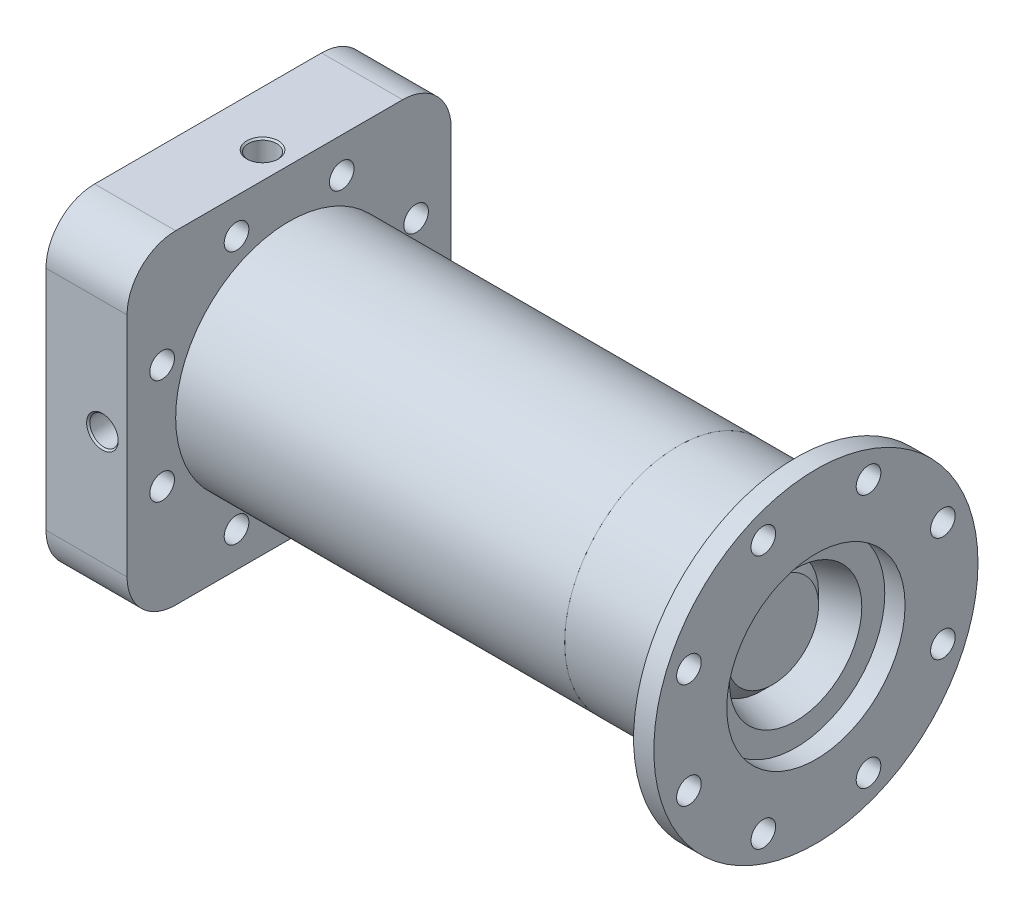
SolidWorks part; units mm, degrees
other "TC"
other "Injector "
other "Volume "
other "Aft O Ring"
other "Forward O ring" parameters "D11"=9.6936, "D1"=8.9273, "D2"=33.6348, "D3"=26.5468, "D4"=23.315, "D5"=33.6348, "D6"=5.8865, "D7"=63.1196, "D8"=7.0953, "D9"=1.4619, "D10"=3.7307, "D12"=6.1926, "D13"=4.361, "D14"=3.81, "D15"=11.3511, "D16"=3.7343, "D17"=3.7343, "D18"=7.0449
ref_plane "Front Plane" through (0, 0, 0) normal (0, 0, 1) x (1, 0, 0)
ref_plane "Top Plane" through (0, 0, 0) normal (0, 1, 0) x (1, 0, 0)
ref_plane "Right Plane" through (0, 0, 0) normal (1, 0, 0) x (0, 0, -1)
sketch "Chamber Revolve" plane through (0, 0, 0) normal (0, 0, 1) x (1, 0, 0)
  line L1 (223.9623, 63.5) -> (223.9623, 25.908)
  line L4 (189.463, 17.9788) -> (173.5582, 33.8836)
  line L5 (173.5582, 33.8836) -> (0, 33.8836)
  line L10 (0, 33.8836) -> (0, 42.5196)
  line L11 (0, 63.5) -> (10.16, 63.5)
  line L12 (10.16, 63.5) -> (10.16, 47.5996)
  line L13 (0, 0) -> (66.3921, 0) construction
  line L15 (191.9165, 17.3214) -> (223.9623, 25.908)
  line L16 (10.16, 47.5996) -> (24.13, 47.5996)
  line L17 (24.13, 47.5996) -> (24.13, 63.5)
  line L18 (24.13, 63.5) -> (223.9623, 63.5)
  line L19 (190.5, 16.9418) -> (191.9165, 17.3214) construction
  line L20 (190.5, 16.9418) -> (189.463, 17.9788) construction
  line L21 (0, 48.5902) -> (3.8608, 48.5902)
  line L22 (3.8608, 48.5902) -> (3.8608, 42.5196)
  line L23 (3.8608, 42.5196) -> (0, 42.5196)
  line L24 (0, 48.5902) -> (0, 63.5)
  arc A0 (189.463, 17.9788) -> (191.9165, 17.3214) centre (191.2591, 19.7748) ccw
  dimension "D11" = 2.54
  dimension "D2" = 67.7672
  dimension "D3" = 51.816
  dimension "D6" = 45
  dimension "D13" = 10.16
  dimension "D8" = 33.8836
  dimension "D9" = 33.4623
  dimension "D7" = 13.716
  dimension "D15" = 13.97
  dimension "D5" = 190.5
  dimension "D4" = 15
  dimension "D18" = 6.0706
  dimension "D12" = 127
revolve "Revolve1" add sketch "Chamber Revolve" angle 360 about L13
fillet "Fillet1" radius 1.27 2 edges at (24.13, 0, 47.5996) (10.16, 0, 47.5996)
sketch "Sketch2" plane through (0, 0, 0) normal (-1, 0, 0) x (0, 0, 1)
  line L0 (0, 0) -> (-24.3004, 58.6664) construction
  line L1 (0, 0) -> (0, 56.6825) construction
  circle A0 centre (-21.7732, 52.565) radius 3.81
  circle A1 centre (0, 0) radius 63.5 construction
  dimension "D2" = 7.62
  dimension "D1" = 6.604
  dimension "D3" = 22.5
extrude "Cut-Extrude1" cut sketch "Sketch2" against normal up to next
pattern_circular "CirPattern1" count 8 over 360 about axis through (0, 0, 0) along (1, 0, 0) of "Cut-Extrude1"
sketch "Sketch4" plane through (0, 0, 0) normal (-1, 0, 0) x (0, 0, 1)
  circle A0 centre (0, 0) radius 63.5
  circle A1 centre (0, 0) radius 63.5 construction
extrude "Boss-Extrude1" add sketch "Sketch4" along normal blind 31.75 separate body
sketch "Sketch5" plane through (0, 0, 0) normal (1, 0, 0) x (0, 0, -1)
  circle A0 centre (21.7732, 52.565) radius 3.81 construction
  circle A1 centre (21.7732, 52.565) radius 3.81
sketch "Sketch11" plane through (-31.75, 0, 0) normal (-1, 0, 0) x (0, 0, 1)
  line L1 (-63.5, -63.5) -> (63.5, -63.5)
  line L2 (-63.5, -63.5) -> (-63.5, 63.5)
  line L3 (-63.5, 63.5) -> (63.5, 63.5)
  line L4 (63.5, -63.5) -> (63.5, 63.5)
  circle A0 centre (0, 0) radius 63.5 construction
  circle A1 centre (0, 0) radius 63.5
  point P6 (0, 63.5)
  point P9 (-63.5, 0)
  circle M18 centre (0, 0) radius 63.5
  dimension "D1" = 127
extrude "Boss-Extrude2" add sketch "Sketch11" against normal up to surface (31.75 mm away) contours L3 L2 L1 M18 | L1 L4 L3 M18 | L4 L3 M18 | L2 L1 M18 up to face at (0, 0, 63.5)
sketch "Sketch12" plane through (0, 0, 0) normal (1, 0, 0) x (0, 0, -1)
  circle A0 centre (0, 0) radius 24.13
  dimension "D1" = 48.26
extrude "Cut-Extrude4" cut sketch "Sketch12" against normal blind 16.51
sketch "Sketch13" plane through (0, 0, 63.5) normal (0, 0, 1) x (1, 0, 0)
  line L1 (0, 63.5) -> (0, -63.5) construction
  line L2 (73.3425, 0) -> (-73.3425, 0) construction
  circle A0 centre (-9.652, 0) radius 1.9685
  dimension "D1" = 3.937
  dimension "D2" = 9.652
extrude "Cut-Extrude5" cut sketch "Sketch13" against normal up to next and the other way through all
sketch "Sketch14" plane through (0, 0, 0) normal (1, 0, 0) x (0, 0, -1)
  line L0 (-63.5, 63.5) -> (63.5, 63.5) construction
  line L1 (-63.5, -63.5) -> (63.5, -63.5) construction
  line L2 (-12.7, 63.5) -> (-63.5, 63.5)
  line L3 (-63.5, 63.5) -> (-63.5, -63.5)
  line L4 (-63.5, -63.5) -> (-12.7, -63.5)
  arc A0 (-12.7, 63.5) -> (-12.7, -63.5) centre (0, 0) ccw
  circle A1 centre (0, 0) radius 63.5 construction
  dimension "D1" = 12.7
chamfer "Chamfer1" distance 4.572 angle 45 1 edges at (0, 0, -24.13)
sketch "Sketch18" plane through (0, 0, 63.5) normal (0, 0, 1) x (1, 0, 0)
  point P0 (-9.652, 0)
hole_wizard "7/16 (0.4375) Diameter Hole1" positions "Sketch18" profile "Sketch20" hole size "7/16" standard "ANSI Inch"
sketch "Sketch20" plane through (-9.652, 0, 63.5) normal (1, 0, 0) x (0, -1, 0)
  line L0 (0, 0) -> (0, 22.3885)
  line L1 (0, 22.3885) -> (5.5562, 19.05)
  line L2 (5.5562, 19.05) -> (5.5562, 0.635)
  line L3 (5.5562, 0.635) -> (6.1912, 0)
  line L5 (6.1912, 0) -> (0, 0)
  line L6 (-5.5562, 0.635) -> (-6.1912, 0) construction
  line L10 (0, 22.3885) -> (-5.5563, 19.05) construction
  line L11 (0, -6.35) -> (0, 107.95) construction
  dimension "Hole Dia." = 11.1125
  dimension "Hole Depth" = 19.05
  dimension "Near C'Sink Dia." = 12.3825
  dimension "Near C'Sink Angle" = 90
  dimension "Drill Angle" = 118
mirror "Mirror1" about plane through (0, 0, 0) normal (0, 0, 1) of "7/16 (0.4375) Diameter Hole1", "Cut-Extrude5"
sketch "Sketch21" plane through (0, 0, 0) normal (0, 1, 0) x (1, 0, 0)
  line L0 (0, 33.8836) -> (173.5582, 33.8836)
  line L1 (0, 42.5196) -> (0, -42.5196) construction
  line L2 (0, 33.8836) -> (0, -33.8836) construction
  line L3 (173.5582, -33.8836) -> (173.5582, 33.8836) construction
  line L4 (173.5582, 33.8836) -> (189.463, 17.9788)
  line L5 (189.463, -17.9788) -> (189.463, 17.9788) construction
  line L6 (189.463, 17.9788) -> (189.463, 0)
  line L10 (0, 0) -> (0, 33.8836)
  line L11 (0, 0) -> (189.463, 0)
  line L12 (189.463, 0) -> (214.4295, 0) construction
revolve "Revolve2" add sketch "Sketch21" angle 360 about L12
fillet "Fillet2" radius 0.889 2 edges at (3.8608, 0, 42.5196) (3.8608, 0, 48.5902)
sketch "Sketch22" plane through (-31.75, 0, 0) normal (-1, 0, 0) x (0, 0, 1)
  point P0 (0, -33.02)
  dimension "D1" = 33.02
hole_wizard "Ø6.7 (6.7) Diameter Hole1" positions "Sketch22" profile "Sketch23" hole size "Ø6.7" standard "ANSI Metric"
sketch "Sketch23" plane through (-31.75, -33.02, 0) normal (0, 1, 0) x (0, 0, 1)
  line L0 (0, 0) -> (0, 15.2209)
  line L1 (0, 15.2209) -> (3.35, 13.208)
  line L2 (3.35, 13.208) -> (3.35, 0.4)
  line L3 (3.35, 0.4) -> (3.75, 0)
  line L5 (3.75, 0) -> (0, 0)
  line L6 (-3.35, 0.4) -> (-3.75, 0) construction
  line L10 (0, 15.2209) -> (-3.35, 13.208) construction
  line L11 (0, -6.35) -> (0, 107.95) construction
  dimension "Hole Dia." = 6.7
  dimension "Hole Depth" = 13.208
  dimension "Near C'Sink Dia." = 7.5
  dimension "Near C'Sink Angle" = 90
  dimension "Drill Angle" = 118
mirror "Mirror2" about plane through (0, 0, 0) normal (0, 1, 0) of "Ø6.7 (6.7) Diameter Hole1"
sketch "Sketch24" plane through (0, 0, 0) normal (0, 1, 0) x (1, 0, 0)
  line L0 (-31.75, 63.5) -> (-31.75, -63.5) construction
  line L1 (-31.75, 7.1374) -> (-30.9581, 5.7658)
  line L2 (-30.9581, 5.7658) -> (-29.845, 5.7658)
  line L3 (-29.4858, 5.617) -> (-28.7329, 4.8641)
  line L4 (-28.7329, 4.8641) -> (-16.51, 4.8641)
  line L5 (-16.51, -24.13) -> (-16.51, 24.13) construction
  line L6 (-16.51, 4.8641) -> (-16.51, 0)
  line L7 (-16.51, 0) -> (-31.75, 0)
  line L8 (-31.75, 0) -> (-31.75, 7.1374)
  line L9 (-29.845, 5.7658) -> (-29.6346, 5.7658) construction
  line L10 (-29.6346, 5.7658) -> (-29.4858, 5.617) construction
  line L11 (-31.75, 0) -> (-56.3457, 0) construction
  arc A0 (-29.845, 5.7658) -> (-29.4858, 5.617) centre (-29.845, 5.2578) cw
  dimension "D2" = 0.508
  dimension "D1" = 60
  dimension "D3" = 4.8641
  dimension "D4" = 7.1374
  dimension "D5" = 5.7658
  dimension "D6" = 1.905
  dimension "D7" = 45
  dimension "D8" = 15.24
ref_axis "Axis1" through (223.9623, 0, 0) along (-1, 0, 0)
revolve "Cut-Revolve1" cut sketch "Sketch24" angle 360 about axis through (223.9623, 0, 0) along (-1, 0, 0)
fillet "Fillet3" radius 0.508 1 edges at (-30.9581, 0, -5.7658)
sketch "Sketch25" plane through (0, 0, 0) normal (0, 0, 1) x (1, 0, 0)
  line L0 (0, -63.5) -> (-31.75, -63.5) construction
  line L1 (0, -63.5) -> (-31.75, -63.5) construction
  line L2 (-4.318, -63.5) -> (-5.4699, -62.8349)
  line L3 (-5.588, -62.6304) -> (-5.588, -61.468)
  line L4 (-11.43, -26.67) -> (-9.398, -26.67)
  line L5 (-5.7368, -61.1088) -> (-6.604, -60.2416)
  line L6 (-6.604, -60.2416) -> (-6.604, -46.8376)
  line L7 (-11.43, -63.5) -> (-11.43, -26.67)
  line L8 (-16.51, -24.13) -> (-16.51, 24.13) construction
  line L9 (-6.604, -46.8376) -> (-9.398, -45.1588)
  line L10 (-9.398, -45.1588) -> (-9.398, -26.67)
  line L11 (-16.51, -24.13) -> (-16.51, 24.13) construction
  line L12 (-11.43, -63.5) -> (-4.318, -63.5)
  line L13 (-11.43, -63.5) -> (-11.43, -73.7659) construction
  arc A1 (-5.588, -61.468) -> (-5.7368, -61.1088) centre (-6.096, -61.468) ccw
  arc A2 (-5.4699, -62.8349) -> (-5.588, -62.6304) centre (-5.3518, -62.6304) cw
  dimension "D4" = 0.2362
  dimension "D6" = 0.508
  dimension "D1" = 7.112
  dimension "D2" = 5.08
  dimension "D3" = 60
  dimension "D5" = 5.842
  dimension "D7" = 45
  dimension "D8" = 2.032
  dimension "D9" = 4.826
  dimension "D10" = 16.6624
  dimension "D11" = 59
  dimension "D12" = 2.032
  dimension "D13" = 2.54
sketch "Sketch29" plane through (0, -63.5, 0) normal (0, -1, 0) x (-1, 0, 0)
  line L0 (0, -63.5) -> (0, 63.5) construction
  point P0 (10.414, 0)
  dimension "D1" = 10.414
hole_wizard "7/16 (0.4375) Diameter Hole2" positions "Sketch29" profile "Sketch30" hole size "7/16" standard "ANSI Inch"
sketch "Sketch30" plane through (-10.414, -63.5, 0) normal (1, 0, 0) x (0, 0, -1)
  line L0 (0, 0) -> (0, 22.3885)
  line L1 (0, 22.3885) -> (5.5562, 19.05)
  line L2 (5.5562, 19.05) -> (5.5562, 0.635)
  line L3 (5.5562, 0.635) -> (6.1913, 0)
  line L5 (6.1913, 0) -> (0, 0)
  line L6 (-5.5562, 0.635) -> (-6.1913, 0) construction
  line L10 (0, 22.3885) -> (-5.5563, 19.05) construction
  line L11 (0, -6.35) -> (0, 107.95) construction
  dimension "Hole Dia." = 11.1125
  dimension "Hole Depth" = 19.05
  dimension "Near C'Sink Dia." = 12.3825
  dimension "Near C'Sink Angle" = 90
  dimension "Drill Angle" = 118
sketch "Sketch31" plane through (0, -63.5, 0) normal (0, -1, 0) x (1, 0, 0)
  circle A0 centre (-10.414, 0) radius 1.5875
  dimension "D1" = 3.175
extrude "Cut-Extrude9" cut sketch "Sketch31" against normal up to surface (39.4223 mm away)
mirror "Mirror3" about plane through (0, 0, 0) normal (0, 1, 0) of "Cut-Extrude9", "7/16 (0.4375) Diameter Hole2"
delete or keep bodies "Body-Delete/Keep 1" type delete bodies bodies 103
sketch "Sketch37" plane through (0, 0, 0) normal (1, 0, 0) x (0, 0, -1)
  line L0 (-63.5, -63.5) -> (63.5, -63.5) construction
  line L1 (-63.5, 63.5) -> (63.5, 63.5) construction
  line L2 (63.5, 63.5) -> (63.5, -63.5) construction
  line L3 (-63.5, 63.5) -> (-63.5, -63.5) construction
  line L4 (-63.5, -63.5) -> (63.5, -63.5)
  line L5 (-63.5, 63.5) -> (63.5, 63.5)
  line L6 (63.5, 63.5) -> (63.5, -63.5)
  line L7 (-63.5, 63.5) -> (-63.5, -63.5)
  circle A0 centre (0, 0) radius 43.688
  dimension "D1" = 87.376
sketch "Sketch32" plane through (0, 0, 0) normal (1, 0, 0) x (0, 0, -1)
  circle A0 centre (0, 0) radius 44.45
  circle A1 centre (0, 0) radius 69.85
  dimension "D1" = 88.9
  dimension "D2" = 139.7
sketch "Sketch33" plane through (0, 0, 0) normal (1, 0, 0) x (0, 0, -1)
  circle A0 centre (0, 0) radius 34.925
  circle A1 centre (0, 0) radius 44.45
  dimension "D1" = 69.85
  dimension "D2" = 88.9
extrude "Boss-Extrude4" add sketch "Sketch33" along normal blind 152.4 separate body
sketch "Sketch34" plane through (0, 0, 0) normal (0, 0, 1) x (1, 0, 0)
  line L2 (152.4, 44.45) -> (152.4, 34.925)
  line L6 (152.4, 34.925) -> (164.992, 16.9418)
  line L7 (164.992, 16.9418) -> (198.4543, 25.908)
  line L8 (198.4543, 25.908) -> (198.4543, 44.45)
  line L9 (198.4543, 44.45) -> (152.4, 44.45)
  line L10 (154.0002, 0) -> (250.6574, 0) construction
  line L11 (152.4, -34.925) -> (152.4, 34.925) construction
  line L12 (152.4, -44.45) -> (152.4, 44.45) construction
  line L13 (152.4, -34.925) -> (152.4, 34.925) construction
  line L14 (152.4, -44.45) -> (152.4, 44.45) construction
  dimension "D1" = 33.8836
  dimension "D2" = 51.816
  dimension "D3" = 15
  dimension "D7" = 55
ref_axis "Axis2" through (152.4, 0, 0) along (-1, 0, 0)
revolve "Revolve3" add sketch "Sketch34" angle 360 about axis through (152.4, 0, 0) along (-1, 0, 0)
fillet "Fillet5" radius 1.27 1 edges at (164.992, 0, -16.9418)
sketch "Sketch35" plane through (0, 0, 0) normal (1, 0, 0) x (0, 0, -1)
  line L0 (0, 0) -> (0, 81.6848) construction
  line L1 (0, 0) -> (18.5655, 44.8211) construction
  line L2 (17.0103, 41.0664) -> (18.5655, 44.8211) construction
  circle A0 centre (18.5655, 44.8211) radius 4.064
  circle A1 centre (0, 0) radius 44.45 construction
  dimension "D1" = 8.128
  dimension "D2" = 22.5
  dimension "D3" = 4.064
fillet "Fillet6" radius 19.05 4 edges at (-15.875, -63.5, 63.5) (-15.875, -63.5, -63.5) (-15.875, 63.5, -63.5) (-15.875, 63.5, 63.5)
sketch "Sketch39" plane through (198.4543, 0, 0) normal (1, 0, 0) x (0, 0, -1)
  circle A0 centre (0, 0) radius 34.925
  circle A1 centre (0, 0) radius 63.5
  dimension "D1" = 69.85
  dimension "D2" = 127
extrude "Boss-Extrude6" add sketch "Sketch39" along normal blind 7.9375 separate body
sketch "Sketch40" plane through (198.4543, 0, 0) normal (-1, 0, 0) x (0, 0, 1)
  line L0 (0, 0) -> (0, 54.3419) construction
  line L1 (0, 0) -> (-20.6067, 49.7491) construction
  circle A0 centre (-20.6067, 49.7491) radius 4.826
  dimension "D2" = 9.652
  dimension "D1" = 22.5
  dimension "D3" = 53.848
extrude "Cut-Extrude13" cut sketch "Sketch40" along normal through all both and the other way through all
pattern_circular "CirPattern3" count 8 over 360 about axis through (0, 0, 0) along (1, 0, 0) of "Cut-Extrude13"
sketch "Sketch41" plane through (0, 0, 0) normal (0, 0, 1) x (1, 0, 0)
  line L0 (0, 37.338) -> (-2.1844, 37.338)
  line L1 (0, 44.45) -> (0, -44.45) construction
  line L2 (-2.6416, 37.7952) -> (-2.6416, 40.9702)
  line L3 (-2.1844, 41.4274) -> (0, 41.4274)
  line L4 (0, 0) -> (38.5106, 0) construction
  line L5 (-2.6416, 41.4274) -> (-2.1844, 41.4274) construction
  line L6 (-2.6416, 40.9702) -> (-2.6416, 41.4274) construction
  line L7 (-2.6416, 37.338) -> (-2.6416, 37.7952) construction
  line L8 (-2.1844, 37.338) -> (-2.6416, 37.338) construction
  line L9 (0, 37.338) -> (0, 41.4274)
  arc A0 (-2.1844, 41.4274) -> (-2.6416, 40.9702) centre (-2.1844, 40.9702) ccw
  arc A1 (-2.6416, 37.7952) -> (-2.1844, 37.338) centre (-2.1844, 37.7952) ccw
  point P15 (0, 41.4036)
  dimension "D4" = 0.4572
  dimension "D1" = 4.0894
  dimension "D2" = 2.6416
  dimension "D3" = 41.4274
revolve "Cut-Revolve2" cut sketch "Sketch41" angle 360 about L4
sketch "Sketch43" plane through (0, 0, 0) normal (0, 0, 1) x (1, 0, 0)
  circle A0 centre (-1.1621, 39.5944) radius 1.3347
sketch "Sketch44" plane through (0, 0, 0) normal (0, 0, 1) x (1, 0, 0)
  line L0 (-2.6416, -40.9702) -> (-2.6416, 40.9702) construction
  line L1 (-2.6416, -40.9702) -> (-2.6416, 40.9702) construction
  line L2 (-2.1844, 41.4274) -> (-2.1844, -41.4274) construction
  line L3 (-2.1844, 41.4274) -> (-2.1844, -41.4274) construction
  line L4 (-2.1844, 41.4274) -> (-6.4254, 41.4274) construction
  circle A0 centre (-0.8763, 39.6621) radius 1.7653
  dimension "D1" = 3.5306
revolve "Revolve4" add sketch "Sketch44" angle 360 about L4
ref_plane "Plane1" through (76.2, 0, 0) normal (1, 0, 0) x (0, 0, -1)
sketch "Sketch45" plane through (0, 0, 0) normal (0, 0, 1) x (1, 0, 0)
  line L0 (152.4, 41.4274) -> (154.5336, 41.4274)
  line L1 (152.4, -44.45) -> (152.4, 44.45) construction
  line L2 (155.0416, 40.9194) -> (155.0416, 37.846)
  line L3 (154.5336, 37.338) -> (152.4, 37.338)
  line L4 (152.4, 41.4274) -> (152.4, 37.338)
  line L5 (152.4, 39.3827) -> (151.151, 39.3827) construction
  line L6 (154.5336, 41.4274) -> (155.0416, 41.4274) construction
  line L7 (155.0416, 41.4274) -> (155.0416, 40.9194) construction
  line L8 (155.0416, 37.846) -> (155.0416, 37.338) construction
  line L9 (155.0416, 37.338) -> (154.5336, 37.338) construction
  arc A0 (154.5336, 41.4274) -> (155.0416, 40.9194) centre (154.5336, 40.9194) cw
  arc A1 (154.5336, 37.338) -> (155.0416, 37.846) centre (154.5336, 37.846) ccw
  dimension "D3" = 41.4274
  dimension "D4" = 0.508
  dimension "D1" = 2.6416
  dimension "D2" = 4.0894
revolve "Cut-Revolve3" cut sketch "Sketch45" angle 360 about L4
mirror "Mirror9" about plane through (76.2, 0, 0) normal (1, 0, 0) of bodies 157
equation "\"Throat Diameter\"= 1.334"
equation "\"Exit Diameter\"= 2.04"
equation "\"D3@Chamber Revolve\"=\"Exit Diameter\""
equation "\"D8@Chamber Revolve\"=\"Throat Diameter\""
equation "\"Injector Ox D\"= 3mm"
equation "\"Injector Fuel D\"= 2mm"
equation "\"Chamber Diameter\"= \"Chamber Throat D Ratio\" * ( \"Throat Diameter\" )"
equation "\"Chamber Throat D Ratio\"= 2"
equation "\"L*\"= 30"
equation "\"Lc\"= \"L*\" / ( \"Chamber Throat D Ratio\" ^ 2 )"
equation "\"T_min\"= 2 * .17"
equation "\"D2@Chamber Revolve\"=\"Chamber Diameter\""
equation "\"D7@Chamber Revolve\"=\"T_min\" +.2"
equation "\"D5@Chamber Revolve\"=\"Lc\""
equation "\"No Flange Holes\"= 8"
equation "\"D1@CirPattern1\"=\"No Flange Holes\""
equation "\"D16@Chamber Revolve\"=\"T_min\""
equation "\"D1@Sketch34\"=\"Throat Diameter\""
equation "\"D2@Sketch34\"=\"Exit Diameter\""
equation "\"D3@Sketch35\"=\"D1@Sketch35\"/2"
equation "\"O ring Groove Width\"= .161"
equation "\"Oring Groove Depth\"= .104"
equation "\"O ring Od\"=3.262"
equation "\"D3@Sketch41\"=\"O ring Od\"/2"
equation "\"D1@Sketch41\"=\"O ring Groove Width\""
equation "\"D2@Sketch41\"=\"Oring Groove Depth\""
equation "\"Corner Rad O ring\"= .018"
equation "\"D4@Sketch41\"=\"Corner Rad O ring\""
equation "\"D1@Sketch45\"=\"Oring Groove Depth\""
equation "\"D2@Sketch45\"=\"O ring Groove Width\""
equation "\"D3@Sketch45\"=\"O ring Od\"/2"
